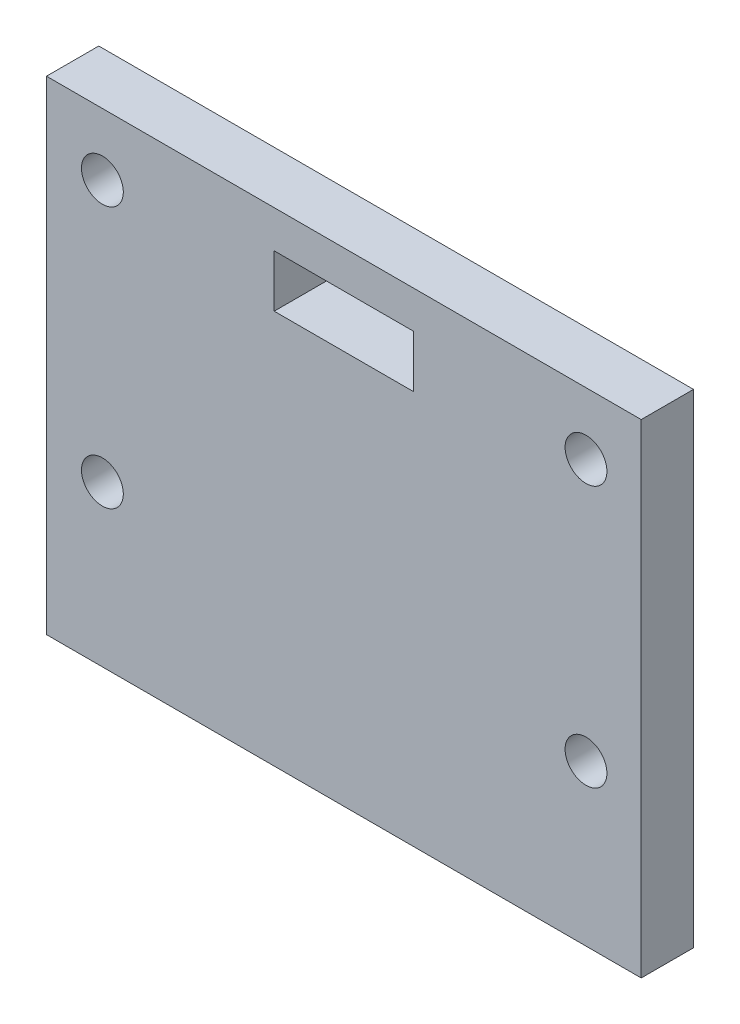
SolidWorks part; units mm, degrees
ref_plane "Front Plane" through (0, 0, 0) normal (0, 0, 1) x (1, 0, 0)
ref_plane "Top Plane" through (0, 0, 0) normal (0, 1, 0) x (1, 0, 0)
ref_plane "Right Plane" through (0, 0, 0) normal (1, 0, 0) x (0, 0, -1)
sketch "Sketch1" plane through (0, 0, 0) normal (0, 0, 1) x (1, 0, 0)
  line L1 (0, 0) -> (45.5, 0)
  line L2 (0, 0) -> (0, 37)
  line L3 (0, 37) -> (45.5, 37)
  line L4 (45.5, 0) -> (45.5, 37)
  line L7 (17.42, 34.14) -> (28.08, 34.14)
  line L8 (17.42, 34.14) -> (17.42, 30.14)
  line L9 (17.42, 30.14) -> (28.08, 30.14)
  line L10 (28.08, 34.14) -> (28.08, 30.14)
  line L11 (17.42, 34.14) -> (28.08, 30.14) construction
  line L12 (17.42, 30.14) -> (28.08, 34.14) construction
  line L13 (17.42, 30.14) -> (28.08, 30.14) construction
  point P4 (22.75, 18.5)
  point P11 (22.75, 32.14)
  dimension "D1" = 4
  dimension "D2" = 10.66
  dimension "D3" = 17.42
  dimension "D4" = 30.14
extrude "Boss-Extrude1" add sketch "Sketch1" along normal blind 4
sketch "Sketch3" plane through (0, 0, 0) normal (0, 0, 1) x (1, 0, 0)
  line L5 (0.0517, 0) -> (45.5, 0) construction
  line L6 (4.2758, 32.2526) -> (41.2758, 32.2526) construction
  line L7 (4.2758, 32.2526) -> (4.2758, 12.2526) construction
  line L8 (4.2758, 12.2526) -> (41.2758, 12.2526) construction
  line L9 (41.2758, 12.2526) -> (41.2758, 32.2526) construction
  circle A0 centre (41.2758, 32.2526) radius 1.6
  circle A1 centre (4.2758, 32.2526) radius 1.6
  circle A2 centre (4.2758, 12.2526) radius 1.6
  circle A3 centre (41.2758, 12.2526) radius 1.6
  point P8 (22.7758, 12.2526)
  point P13 (22.7758, 0)
  dimension "D1" = 4.2242
  dimension "D5" = 3.2
  dimension "D2" = 37
  dimension "D3" = 20
  dimension "D4" = 12.2526
extrude "Cut-Extrude5" cut sketch "Sketch3" along normal blind 10 and the other way through all contours A0 | A3 | A2 | A1
